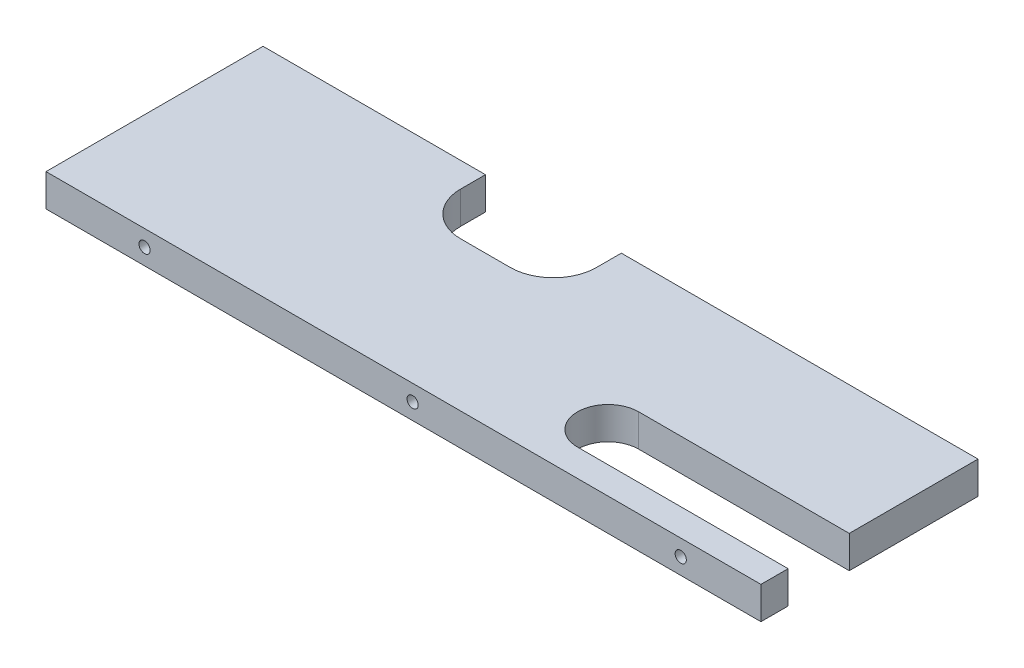
SolidWorks part; units mm, degrees
ref_plane "Front Plane" through (0, 0, 0) normal (0, 0, 1) x (1, 0, 0)
ref_plane "Top Plane" through (0, 0, 0) normal (0, 1, 0) x (1, 0, 0)
ref_plane "Right Plane" through (0, 0, 0) normal (1, 0, 0) x (0, 0, -1)
sketch "Sketch1" plane through (0, 0, 0) normal (0, 0, 1) x (1, 0, 0)
  line L1 (-105.2375, 4.7625) -> (105.2375, 4.7625)
  line L2 (-105.2375, 4.7625) -> (-105.2375, -4.7625)
  line L3 (-105.2375, -4.7625) -> (105.2375, -4.7625)
  line L4 (105.2375, 4.7625) -> (105.2375, -4.7625)
  point P4 (0, 4.7625)
  point P6 (-105.2375, 0)
  dimension "D1" = 210.475
  dimension "D2" = 9.525
extrude "Boss-Extrude1" add sketch "Sketch1" along normal blind 63.9
sketch "Sketch2" plane through (0, 4.7625, 0) normal (0, 1, 0) x (1, 0, 0)
  line L0 (105.2375, 0) -> (-105.2375, 0) construction
  line L1 (-39.7625, 0) -> (0.2375, 0)
  line L2 (-39.7625, 0) -> (-39.7625, -20)
  line L3 (-39.7625, -20) -> (0.2375, -20)
  line L4 (0.2375, 0) -> (0.2375, -20)
  line L5 (105.2375, -63.9) -> (105.2375, 0) construction
  dimension "D1" = 20
  dimension "D2" = 40
  dimension "D3" = 105
extrude "Cut-Extrude1" cut sketch "Sketch2" against normal through all
fillet "Fillet1" radius 12.7 2 edges at (0.2375, 0, 20) (-39.7625, 0, 20)
sketch "Sketch4" plane through (0, 0, 63.9) normal (0, 0, 1) x (1, 0, 0)
  line L0 (105.2375, -4.7625) -> (105.2375, 4.7625) construction
  line L1 (-105.2375, 4.7625) -> (-105.2375, -4.7625) construction
  point P0 (-76.2285, 0)
  point P1 (2.6995, 0)
  point P2 (81.6285, 0)
  point P9 (-105.2375, 0)
  dimension "D1" = 23.609
  dimension "D2" = 78.929
  dimension "D3" = 78.928
hole_wizard "Tap Drill for M4 Tap1" positions "Sketch5" profile "Sketch6" hole size "M4" standard "ISO"
sketch "Sketch5" plane through (0, 0, 63.9) normal (0, 0, 1) x (1, 0, 0)
  point P0 (-76.2285, 0)
  point P3 (2.6995, 0)
  point P6 (81.6285, 0)
sketch "Sketch6" plane through (-76.2285, 0, 63.9) normal (1, 0, 0) x (0, -1, 0)
  line L0 (0, 0) -> (0, 13.6914)
  line L1 (0, 13.6914) -> (1.65, 12.7)
  line L2 (1.65, 12.7) -> (1.65, 0)
  line L5 (1.65, 0) -> (0, 0)
  line L10 (0, 13.6914) -> (-1.65, 12.7) construction
  line L11 (0, -6.35) -> (0, 107.95) construction
  dimension "Hole Dia." = 3.3
  dimension "Hole Depth" = 12.7
  dimension "Drill Angle" = 118
sketch "Sketch7" plane through (0, 4.7625, 0) normal (0, 1, 0) x (1, 0, 0)
  line L0 (105.2375, -63.9) -> (105.2375, 0) construction
  line L1 (43.2375, -37.9) -> (105.2375, -37.9)
  line L3 (43.2375, -55.9) -> (105.2375, -55.9)
  line L4 (105.2375, -37.9) -> (105.2375, -55.9)
  line L5 (105.2375, -46.9) -> (43.2375, -46.9) construction
  line L6 (105.2375, -63.9) -> (-105.2375, -63.9) construction
  arc A0 (43.2375, -37.9) -> (43.2375, -55.9) centre (43.2375, -46.9) ccw
  dimension "D1" = 17
  dimension "D2" = 18
  dimension "D3" = 62
extrude "Cut-Extrude2" cut sketch "Sketch7" against normal through all
